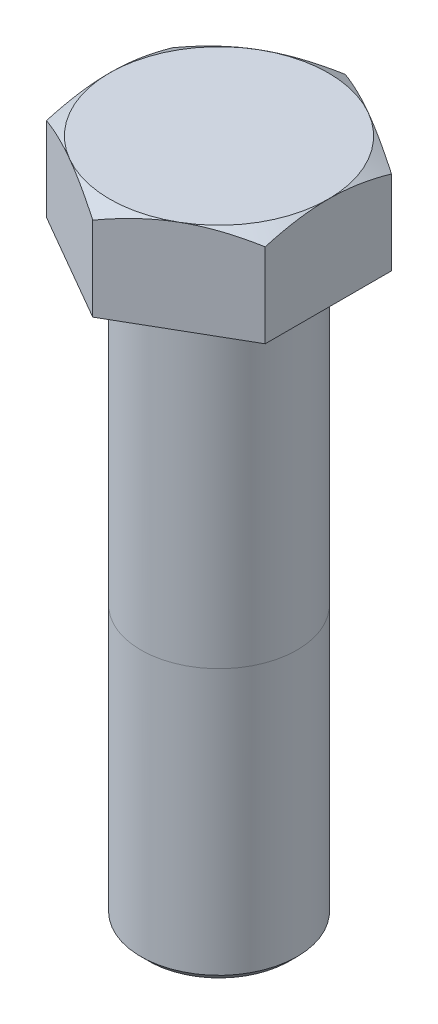
SolidWorks part; units mm, degrees
ref_plane "Front Plane" through (0, 0, 0) normal (0, 0, 1) x (1, 0, 0)
ref_plane "Top Plane" through (0, 0, 0) normal (0, 1, 0) x (1, 0, 0)
ref_plane "Right Plane" through (0, 0, 0) normal (1, 0, 0) x (0, 0, -1)
sketch "Sketch1" plane through (0, 0, 0) normal (0, 1, 0) x (1, 0, 0)
  line L1 (0, -16.1658) -> (14, -8.0829)
  line L2 (14, -8.0829) -> (14, 8.0829)
  line L3 (14, 8.0829) -> (0, 16.1658)
  line L4 (0, 16.1658) -> (-14, 8.0829)
  line L5 (-14, 8.0829) -> (-14, -8.0829)
  line L6 (-14, -8.0829) -> (0, -16.1658)
  circle A0 centre (0, 0) radius 14 construction
  dimension "D1" = 28
extrude "Boss-Extrude1" add sketch "Sketch1" along normal blind 12
sketch "Sketch2" plane through (0, 12, 0) normal (0, 1, 0) x (1, 0, 0)
  line L0 (14, 8.0829) -> (0, 16.1658) construction
  circle A0 centre (0, 0) radius 14
extrude "Cut-Extrude1" cut sketch "Sketch2" against normal blind 12 draft 60 flip side to cut
sketch "Sketch3" plane through (0, 0, 0) normal (0, -1, 0) x (1, 0, 0)
  circle A0 centre (0, 0) radius 10
  dimension "D1" = 20
extrude "Boss-Extrude2" add sketch "Sketch3" along normal blind 75
chamfer "Chamfer1" distance 1 angle 45 1 edges at (0, -75, -10)
sketch "Sketch4" plane through (0, 0, 0) normal (0, 0, 1) x (1, 0, 0)
  line L0 (-10, -40) -> (10, -40)
  line L1 (-10, 0) -> (-10, -74) construction
  line L2 (10, -74) -> (10, 0) construction
  line L3 (-10, 0) -> (10, 0) construction
  dimension "D1" = 40
split line "Split Line1"
